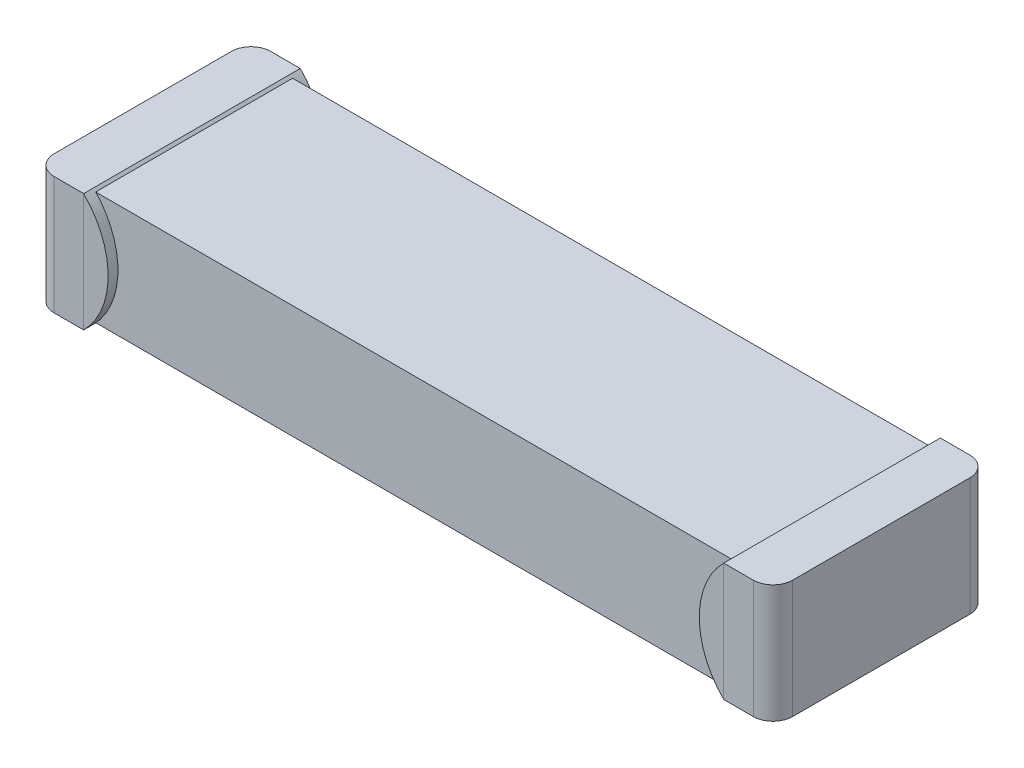
SolidWorks part; units mm, degrees
ref_plane "Front Plane" through (0, 0, 0) normal (0, 0, 1) x (1, 0, 0)
ref_plane "Top Plane" through (0, 0, 0) normal (0, 1, 0) x (1, 0, 0)
ref_plane "Right Plane" through (0, 0, 0) normal (1, 0, 0) x (0, 0, -1)
sketch "Sketch1" plane through (0, 0, 0) normal (0, 1, 0) x (1, 0, 0)
  line L1 (0, 0) -> (7.5, 0)
  line L2 (0, 0) -> (0, 2)
  line L3 (0, 2) -> (7.5, 2)
  line L4 (7.5, 0) -> (7.5, 2)
  dimension "D1" = 7.5
  dimension "D2" = 2
extrude "Boss-Extrude1" add sketch "Sketch1" along normal blind 1.15 from offset 0.025 offset against normal yes
sketch "Sketch2" plane through (0, 0, 0) normal (0, 1, 0) x (1, 0, 0)
  line L0 (0.5, 2.1) -> (7.0001, 2.1)
  line L2 (7.0001, 2.1) -> (7.5001, 2.1)
  line L4 (7.0001, 2.1) -> (7.0001, -0.1)
  line L5 (7.0001, -0.1) -> (7.5001, -0.1)
  line L7 (7.0001, 1.5789) -> (7.0001, 0)
  line L10 (7.5001, 2.1) -> (7.5001, -0.1)
  line L13 (0, 2.1) -> (0.5, 2.1)
  line L14 (0, 2.1) -> (0, -0.1)
  line L15 (0, -0.1) -> (0.5, -0.1)
  line L16 (0.5, 2.1) -> (0.5, -0.1)
extrude "Boss-Extrude2" add sketch "Sketch2" along normal blind 1.2 from offset 0.05 contours L10 L2 L4 L5 | L14 L15 L16 L13 offset against normal yes
fillet "Fillet1" radius 0.2 4 edges at (0, 0.55, -2.1) (0, 0.55, 0.1) (7.5001, 0.55, -2.1) (7.5001, 0.55, 0.1)
sketch "Sketch3" plane through (0, 0, 0.1) normal (0, 0, 1) x (1, 0, 0)
  line L0 (7.0001, 1.15) -> (7.0001, -0.05)
  line L1 (0.5, 1.15) -> (0.5, -0.05)
  arc A0 (7.0001, -0.05) -> (7.0001, 1.15) centre (7.6001, 0.55) cw
  arc A1 (0.5, 1.15) -> (0.5, -0.05) centre (-0.1, 0.55) cw
extrude "Boss-Extrude3" add sketch "Sketch3" against normal blind 2.2 separate body
